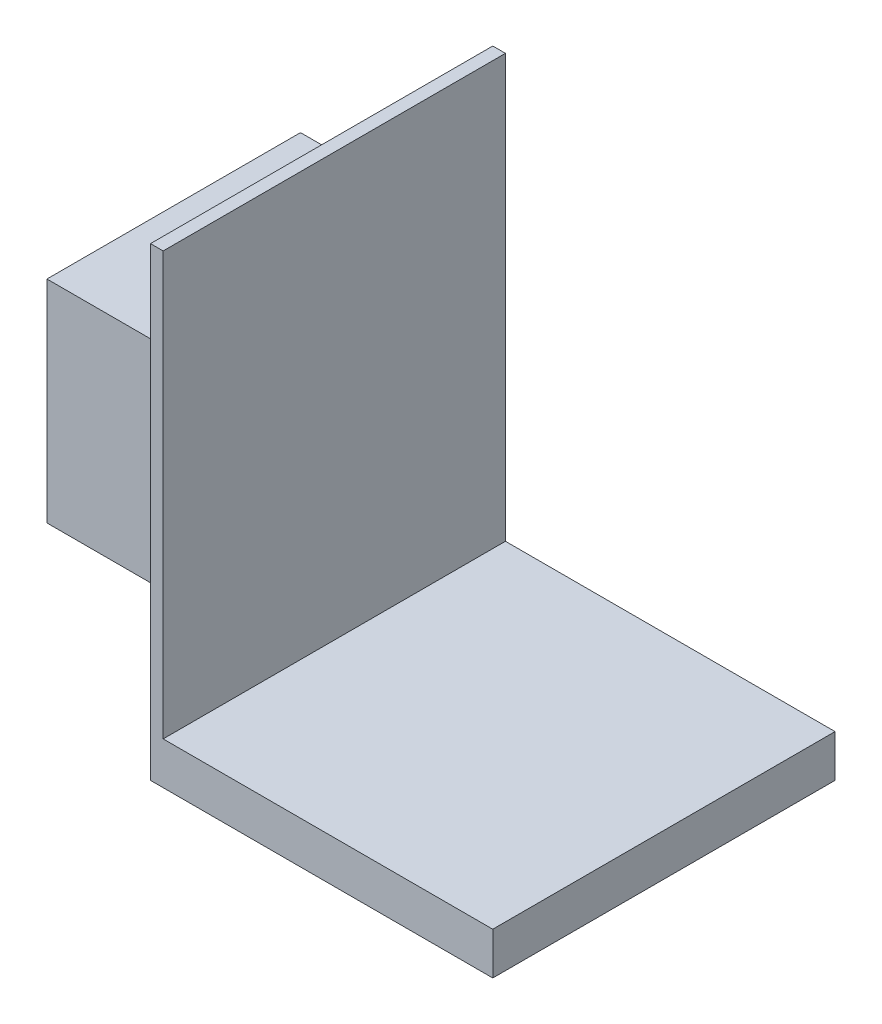
SolidWorks part; units mm, degrees
ref_plane "Front Plane" through (0, 0, 0) normal (0, 0, 1) x (1, 0, 0)
ref_plane "Top Plane" through (0, 0, 0) normal (0, 1, 0) x (1, 0, 0)
ref_plane "Right Plane" through (0, 0, 0) normal (1, 0, 0) x (0, 0, -1)
sketch "Sketch1" plane through (0, 0, 0) normal (0, 1, 0) x (1, 0, 0)
  line L1 (-40.5, -40.5) -> (40.5, -40.5)
  line L2 (-40.5, -40.5) -> (-40.5, 40.5)
  line L3 (-40.5, 40.5) -> (40.5, 40.5)
  line L4 (40.5, -40.5) -> (40.5, 40.5)
  line L5 (-40.5, -40.5) -> (40.5, 40.5) construction
  line L6 (-40.5, 40.5) -> (40.5, -40.5) construction
  point P0 (0, 0)
  dimension "D1" = 81
  dimension "D2" = 81
extrude "Boss-Extrude1" add sketch "Sketch1" along normal blind 10
sketch "Sketch2" plane through (0, 0, 0) normal (0, 1, 0) x (1, 0, 0)
  line L0 (-40.5, -40.5) -> (40.5, -40.5) construction
  line L1 (-40.5, 40.5) -> (-37.5, 40.5)
  line L2 (-40.5, 40.5) -> (-40.5, -40.5)
  line L3 (-40.5, -40.5) -> (-37.5, -40.5)
  line L4 (-37.5, 40.5) -> (-37.5, -40.5)
  dimension "D1" = 3
extrude "Boss-Extrude2" add sketch "Sketch2" along normal blind 100 from surface at 10 starting at face at (0, 10, 0)
sketch "Sketch3" plane through (-40.5, 0, 0) normal (-1, 0, 0) x (0, 0, 1)
  line L0 (-40.5, 110) -> (40.5, 0) construction
  line L1 (-40.5, 0) -> (40.5, 110) construction
  line L3 (-30, 30) -> (30, 30)
  line L4 (-30, 30) -> (-30, 80)
  line L5 (-30, 80) -> (30, 80)
  line L6 (30, 30) -> (30, 80)
  line L7 (-30, 30) -> (30, 80) construction
  line L8 (-30, 80) -> (30, 30) construction
  point P8 (0, 55)
  dimension "D1" = 60
  dimension "D2" = 50
extrude "Boss-Extrude3" add sketch "Sketch3" along normal blind 35
sketch "Sketch4" plane through (0, 80, 0) normal (0, 1, 0) x (1, 0, 0)
  line L0 (-40.5, 30) -> (-55.5, 30) construction
  line L1 (-75.5, 30) -> (-40.5, 30) construction
  line L2 (-55.5, 30) -> (-55.5, 15) construction
  line L4 (-55.5, 15) -> (-55.5, -15) construction
  line L5 (-55.5, -15) -> (-55.5, -30) construction
  line L6 (-75.5, -30) -> (-40.5, -30) construction
  circle A0 centre (-55.5, 15) radius 5
  circle A1 centre (-55.5, -15) radius 5
  dimension "D4" = 10
  dimension "D5" = 10
  dimension "D1" = 15
  dimension "D2" = 15
  dimension "D3" = 30
extrude "Cut-Extrude1" cut sketch "Sketch4" against normal up to next contours A0 | A1
sketch "Sketch5" plane through (0, 0, 30) normal (0, 0, 1) x (1, 0, 0)
  line L0 (-75.5, 55) -> (-40.5, 55) construction
  line L1 (-75.5, 30) -> (-75.5, 80) construction
  line L2 (-40.5, 30) -> (-40.5, 80) construction
  line L3 (-75.5, 75) -> (-75.5, 70)
  line L4 (-75.5, 80) -> (-70.5, 80) construction
  line L5 (-75.5, 80) -> (-75.5, 75) construction
  line L6 (-75.5, 75) -> (-70.5, 75)
  line L7 (-70.5, 80) -> (-70.5, 75)
  line L8 (-70.5, 80) -> (-65.5, 80)
  line L9 (-75.5, 80) -> (-40.5, 80) construction
  line L10 (-65.5, 80) -> (-65.5, 70)
  line L11 (-65.5, 70) -> (-75.5, 70)
  line L12 (-65.5, 30) -> (-65.5, 40)
  line L13 (-70.5, 30) -> (-65.5, 30)
  line L14 (-70.5, 30) -> (-70.5, 35)
  line L15 (-75.5, 35) -> (-70.5, 35)
  line L16 (-75.5, 35) -> (-75.5, 40)
  line L17 (-65.5, 40) -> (-75.5, 40)
  dimension "D1" = 5
  dimension "D2" = 5
  dimension "D3" = 5
  dimension "D4" = 5
extrude "Cut-Extrude4" cut sketch "Sketch5" against normal blind 20 from offset 20 offset against normal yes
